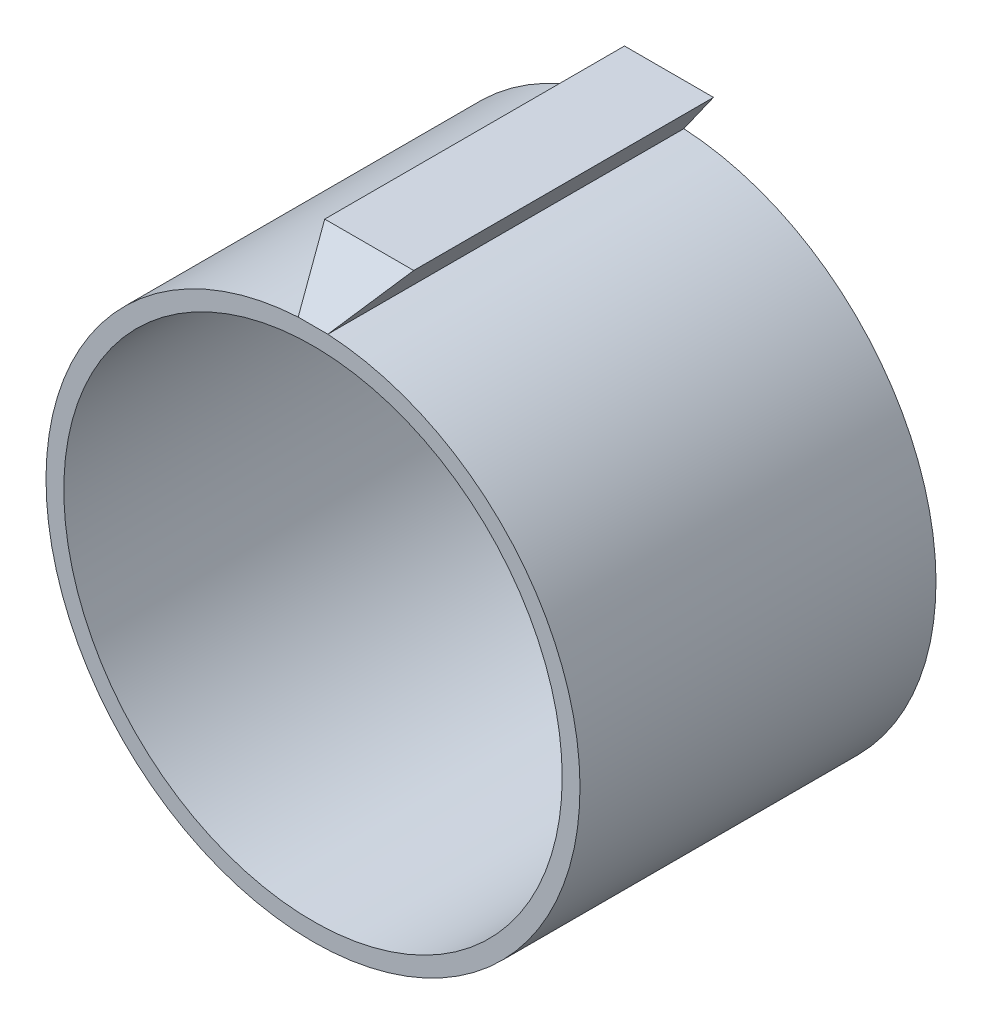
SolidWorks part; units mm, degrees
ref_plane "Front Plane" through (0, 0, 0) normal (0, 0, 1) x (1, 0, 0)
ref_plane "Top Plane" through (0, 0, 0) normal (0, 1, 0) x (1, 0, 0)
ref_plane "Right Plane" through (0, 0, 0) normal (1, 0, 0) x (0, 0, -1)
sketch "Sketch1" plane through (0, 0, 0) normal (0, 0, 1) x (1, 0, 0)
  line L0 (0, 42) -> (0, 52) construction
  line L3 (-7.5, 52) -> (7.5, 52)
  line L4 (-7.5, 52) -> (-2.5, 44.9305)
  line L5 (7.5, 52) -> (2.5, 44.9305)
  circle A0 centre (0, 0) radius 42
  arc A1 (-25, 33.7491) -> (25, 33.7491) centre (0, 0) cw
  arc A2 (26.7857, 36.1597) -> (-2.5, 44.9305) centre (0, 0) cw
  arc A3 (2.5, 44.9305) -> (26.7857, 36.1597) centre (0, 0) cw
  arc A4 (-26.7857, 36.1597) -> (26.7857, 36.1597) centre (0, 0) cw construction
  point P3 (-25, 33.7491)
  point P4 (25, 33.7491)
  point P16 (0, 52)
  point P18 (0, 47)
  dimension "D1" = 84
  dimension "D2" = 50
  dimension "D3" = 10
  dimension "D5" = 15
  dimension "D6" = 2.5
  dimension "D4" = 3
extrude "Boss-Extrude1" add sketch "Sketch1" along normal blind 60 contours A3 L5 L3 L4 A2 A0
sketch "Sketch2" plane through (0, 0, 0) normal (1, 0, 0) x (0, 0, -1)
  line L0 (-60, 44.9305) -> (-50.5251, 52)
  line L1 (-60, 52) -> (0, 52) construction
  line L2 (-50.5251, 52) -> (-60, 52)
  line L3 (-60, 52) -> (-60, 44.9305)
extrude "Cut-Extrude1" cut sketch "Sketch2" along normal up to surface and the other way up to surface up to face at (5, 48.4653, 30) other way up to face at (-5, 48.4653, 30)
